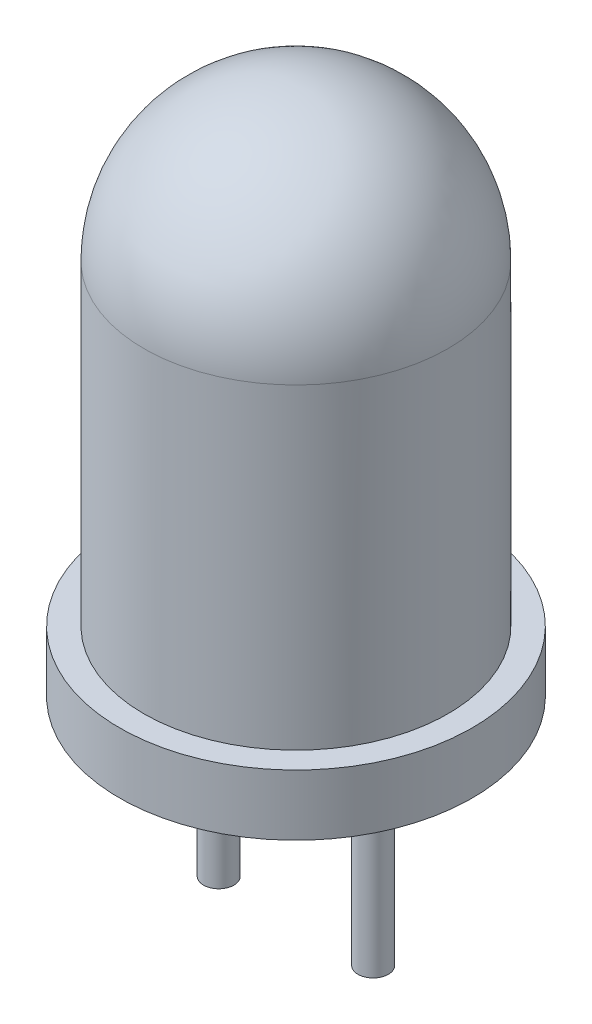
SolidWorks part; units mm, degrees
ref_plane "Front Plane" through (0, 0, 0) normal (0, 0, 1) x (1, 0, 0)
ref_plane "Top Plane" through (0, 0, 0) normal (0, 1, 0) x (1, 0, 0)
ref_plane "Right Plane" through (0, 0, 0) normal (1, 0, 0) x (0, 0, -1)
sketch "Sketch2" plane through (0, 0, 0) normal (0, 0, 1) x (1, 0, 0)
  line L0 (0, 0) -> (0, 8.7) construction
  line L1 (2.5, 6.2) -> (2.5, 1)
  line L2 (2.5, 1) -> (2.9, 1)
  line L3 (2.9, 1) -> (2.9, 0)
  line L4 (2.9, 0) -> (0, 0)
  line L5 (0, 0) -> (0, 8.7)
  arc A0 (0, 8.7) -> (2.5, 6.2) centre (0, 6.2) cw
  dimension "D1" = 1
  dimension "D2" = 5
  dimension "D3" = 5.8
  dimension "D4" = 7.7
revolve "Revolve1" add sketch "Sketch2" angle 360 about L0
sketch "Sketch3" plane through (0, 0, 0) normal (0, 1, 0) x (1, 0, 0)
  line L0 (-1.27, 0) -> (1.27, 0) construction
  circle A0 centre (-1.27, 0) radius 0.25
  circle A1 centre (1.27, 0) radius 0.25
  point P4 (0, 0)
  dimension "D1" = 2.54
  dimension "D2" = 0.5
extrude "Boss-Extrude2" add sketch "Sketch3" against normal blind 3.2 contours A0 | A1
